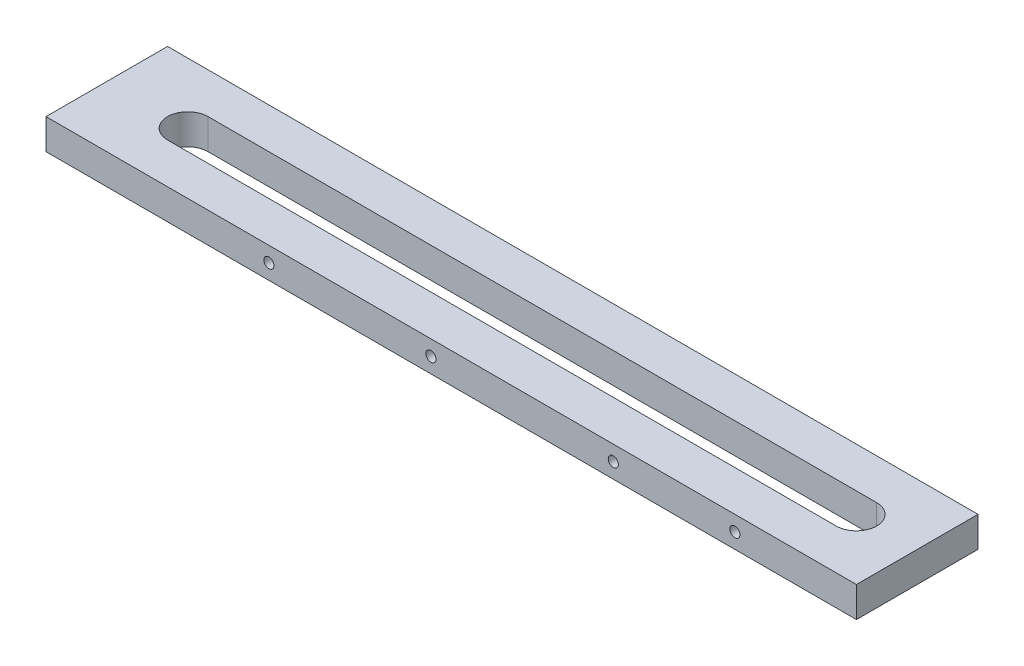
SolidWorks part; units mm, degrees
material "Oak"
ref_plane "Front Plane" through (0, 0, 0) normal (0, 0, 1) x (1, 0, 0)
ref_plane "Top Plane" through (0, 0, 0) normal (0, 1, 0) x (1, 0, 0)
ref_plane "Right Plane" through (0, 0, 0) normal (1, 0, 0) x (0, 0, -1)
other "Configuration Table"
sketch "Sketch1" plane through (0, 0, 0) normal (0, 1, 0) x (1, 0, 0)
  line L1 (-254, 38.1) -> (254, 38.1)
  line L2 (-254, 38.1) -> (-254, -38.1)
  line L3 (-254, -38.1) -> (254, -38.1)
  line L4 (254, 38.1) -> (254, -38.1)
  line L5 (-254, 38.1) -> (254, -38.1) construction
  line L6 (-254, -38.1) -> (254, 38.1) construction
  point P0 (0, 0)
  dimension "D1" = 508
  dimension "D2" = 76.2
extrude "Boss-Extrude1" add sketch "Sketch1" along normal blind 19.05
sketch "Sketch3" plane through (0, 19.05, 0) normal (0, 1, 0) x (1, 0, 0)
  line L0 (-203.2, 0) -> (215.9, 0) construction
  line L1 (-203.2, 12.7) -> (215.9, 12.7)
  line L2 (-203.2, -12.7) -> (215.9, -12.7)
  line L3 (254, -38.1) -> (254, 38.1) construction
  arc A0 (-203.2, 12.7) -> (-203.2, -12.7) centre (-203.2, 0) ccw
  arc A1 (215.9, -12.7) -> (215.9, 12.7) centre (215.9, 0) ccw
  point P3 (6.35, 0)
  dimension "D3" = 12.7
  dimension "D1" = 419.1
  dimension "D2" = 38.1
extrude "Cut-Extrude1" cut sketch "Sketch3" against normal through all
sketch "Sketch5" plane through (0, 0, 38.1) normal (0, 0, 1) x (1, 0, 0)
  line L0 (-190.5, 43.6178) -> (-190.5, -18.6873) construction
  line L1 (-254, 19.05) -> (-254, 0) construction
  line L2 (254, 19.05) -> (254, 0) construction
  line L3 (-254, 19.05) -> (254, 19.05) construction
  circle A0 centre (-114.3, 9.525) radius 3.175
  circle A1 centre (-12.7, 9.525) radius 3.175
  circle A2 centre (101.6, 9.525) radius 3.175
  circle A3 centre (177.8, 9.525) radius 3.175
  dimension "D2" = 6.35
  dimension "D1" = 63.5
  dimension "D3" = 76.2
  dimension "D4" = 76.2
  dimension "D5" = 101.6
  dimension "D6" = 114.3
  dimension "D7" = 76.2
  dimension "D8" = 9.525
  dimension "D9" = 9.525
  dimension "D10" = 9.525
extrude "Cut-Extrude3" cut sketch "Sketch5" against normal blind 12.7
